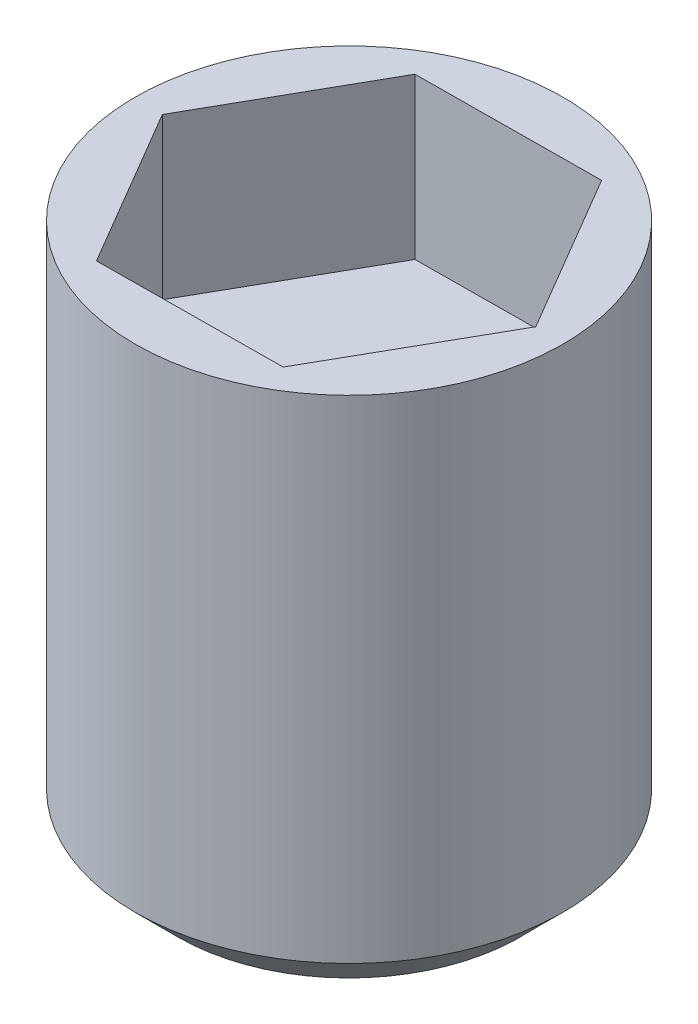
SolidWorks part; units mm, degrees
ref_plane "Спереди" through (0, 0, 0) normal (0, 0, 1) x (1, 0, 0)
ref_plane "Сверху" through (0, 0, 0) normal (0, 1, 0) x (1, 0, 0)
ref_plane "Справа" through (0, 0, 0) normal (1, 0, 0) x (0, 0, -1)
sketch "Эскиз1" plane through (0, 0, 0) normal (0, 0, 1) x (1, 0, 0)
  line L0 (0, 0) -> (3.2, 0)
  line L2 (4, 10) -> (4, 0.8)
  line L3 (4, 0.8) -> (3.2, 0)
  line L4 (4, 10) -> (0, 10)
  line L5 (0, 68.6446) -> (0, -29.1082) construction
  line L6 (0, 0) -> (0, 10)
revolve "Повернуть1" add sketch "Эскиз1" angle 360 about L5
sketch "Эскиз2" plane through (0, 10, 0) normal (0, 1, 0) x (1, 0, 0)
  line L1 (1.7553, -2.9865) -> (3.464, 0.0269)
  line L2 (3.464, 0.0269) -> (1.7087, 3.0133)
  line L3 (1.7087, 3.0133) -> (-1.7553, 2.9865)
  line L4 (-1.7553, 2.9865) -> (-3.464, -0.0269)
  line L5 (-3.464, -0.0269) -> (-1.7087, -3.0133)
  line L6 (-1.7087, -3.0133) -> (1.7553, -2.9865)
  circle A0 centre (0, 0) radius 3 construction
extrude "Вырез-Вытянуть1" cut sketch "Эскиз2" against normal blind 3
